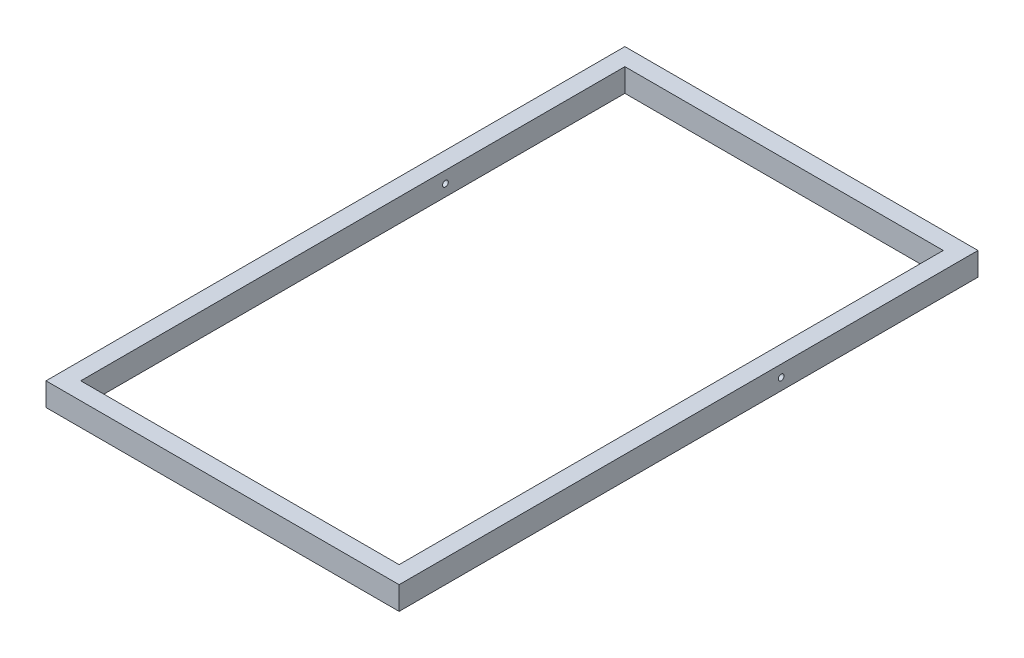
SolidWorks part; units mm, degrees
ref_plane "Спереди" through (0, 0, 0) normal (0, 0, 1) x (1, 0, 0)
ref_plane "Сверху" through (0, 0, 0) normal (0, 1, 0) x (1, 0, 0)
ref_plane "Справа" through (0, 0, 0) normal (1, 0, 0) x (0, 0, -1)
sketch "Эскиз1" plane through (0, 0, 0) normal (0, 1, 0) x (1, 0, 0)
  line L0 (-37.9657, 943.7256) -> (-37.9657, 3.7256)
  line L1 (-37.9657, 3.7256) -> (512.0343, 3.7256)
  line L2 (512.0343, 3.7256) -> (512.0343, 943.7256)
  line L3 (512.0343, 943.7256) -> (-37.9657, 943.7256)
  line L4 (-67.9657, 973.7256) -> (-67.9657, -26.2744)
  line L5 (-67.9657, -26.2744) -> (542.0343, -26.2744)
  line L6 (542.0343, -26.2744) -> (542.0343, 973.7256)
  line L7 (542.0343, 973.7256) -> (-67.9657, 973.7256)
  dimension "D1" = 30
  dimension "D2" = 30
  dimension "D3" = 30
  dimension "D4" = 30
  dimension "D5" = 1000
  dimension "D6" = 550
extrude "Бобышка-Вытянуть1" add sketch "Эскиз1" along normal blind 40
sketch "Эскиз2" plane through (542.0343, 0, 0) normal (1, 0, 0) x (0, 0, -1)
  line L0 (633.7256, 0) -> (633.7256, 40) construction
  line L1 (-26.2744, 0) -> (973.7256, 0) construction
  line L2 (-26.2744, 40) -> (973.7256, 40) construction
  line L3 (973.7256, 40) -> (973.7256, 0) construction
  circle A0 centre (633.7256, 20) radius 5
  dimension "D1" = 10
  dimension "D2" = 340
extrude "Вырез-Вытянуть1" cut sketch "Эскиз2" against normal through all
sketch "Эскиз3" plane through (542.0343, 0, 0) normal (1, 0, 0) x (0, 0, -1)
  line L0 (-26.2744, 20) -> (973.7256, 20) construction
  line L1 (-26.2744, 40) -> (-26.2744, 0) construction
  line L2 (973.7256, 40) -> (973.7256, 0) construction
  line L3 (73.7256, 0) -> (73.7256, 20)
  line L4 (-26.2744, 0) -> (973.7256, 0) construction
  line L5 (113.7256, 0) -> (93.7256, 20)
  line L6 (133.7256, 0) -> (133.7256, 20)
  line L7 (173.7256, 0) -> (153.7256, 20)
  line L8 (73.7256, 0) -> (113.7256, 0)
  line L9 (133.7256, 0) -> (173.7256, 0)
  line L10 (153.7256, 20) -> (133.7256, 20)
  line L11 (193.7256, 0) -> (193.7256, 20)
  line L12 (233.7256, 0) -> (213.7256, 20)
  line L13 (93.7256, 20) -> (73.7256, 20)
  line L14 (193.7256, 0) -> (233.7256, 0)
  line L15 (213.7256, 20) -> (193.7256, 20)
  dimension "D1" = 100
  dimension "D2" = 20
  dimension "D3" = 3
  dimension "D4" = 40
extrude "Вырез-Вытянуть2" [suppressed] cut sketch "Эскиз3" against normal through all
